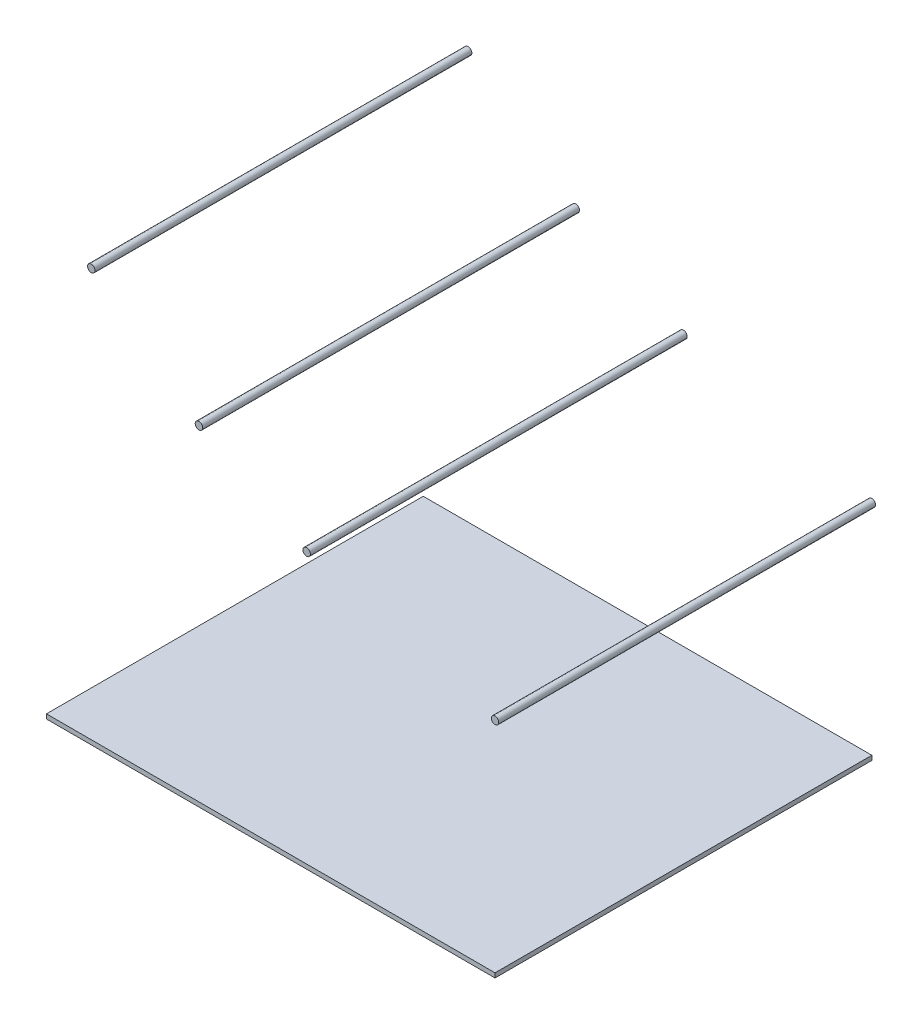
SolidWorks part; units mm, degrees
ref_plane "Front Plane" through (0, 0, 0) normal (0, 0, 1) x (1, 0, 0)
ref_plane "Top Plane" through (0, 0, 0) normal (0, 1, 0) x (1, 0, 0)
ref_plane "Right Plane" through (0, 0, 0) normal (1, 0, 0) x (0, 0, -1)
sketch "Sketch1" plane through (0, 0, 0) normal (0, 0, 1) x (1, 0, 0)
  line L1 (0, 0) -> (-2540, 0)
  line L2 (0, 0) -> (0, -25.4)
  line L3 (0, -25.4) -> (-2540, -25.4)
  line L4 (-2540, 0) -> (-2540, -25.4)
  circle A0 centre (0, 1238.25) radius 21.082
  circle A1 centre (-1066.8, 1530.35) radius 21.082
  circle A2 centre (-1676.4, 1844.675) radius 21.082
  circle A3 centre (-2286, 2311.4) radius 21.082
  dimension "D1" = 42.164
  dimension "D3" = 609.6
  dimension "D4" = 609.6
  dimension "D5" = 1066.8
  dimension "D6" = 1530.35
  dimension "D7" = 1844.675
  dimension "D8" = 2311.4
  dimension "D2" = 1238.25
  dimension "D9" = 25.4
  dimension "D10" = 2540
extrude "Boss-Extrude1" add sketch "Sketch1" along normal mid plane 2133.6
sketch "Sketch2" plane through (0, 0, 0) normal (0, 0, 1) x (1, 0, 0)
  line L0 (-1094.459, 712.0715) -> (-1094.459, 1474.0715)
  line L1 (-1475.459, 1474.0715) -> (-713.459, 1474.0715)
  line L2 (-1475.459, 1474.0715) -> (-1475.459, 407.2715)
  line L3 (-1475.459, 407.2715) -> (-713.459, 407.2715)
  line L4 (-713.459, 1474.0715) -> (-713.459, 407.2715)
  line L5 (-1094.459, 1474.0715) -> (-1094.459, 2185.2715)
  line L6 (-1094.459, 712.0715) -> (-1531.5243, 1336.2654)
  line L7 (-1531.5243, 1336.2654) -> (-1939.4518, 1918.8463)
  dimension "D1" = 1066.8
  dimension "D2" = 762
  dimension "D3" = 762
  dimension "D4" = 381
  dimension "D5" = 304.8
  dimension "D6" = 711.2
  dimension "D7" = 35
